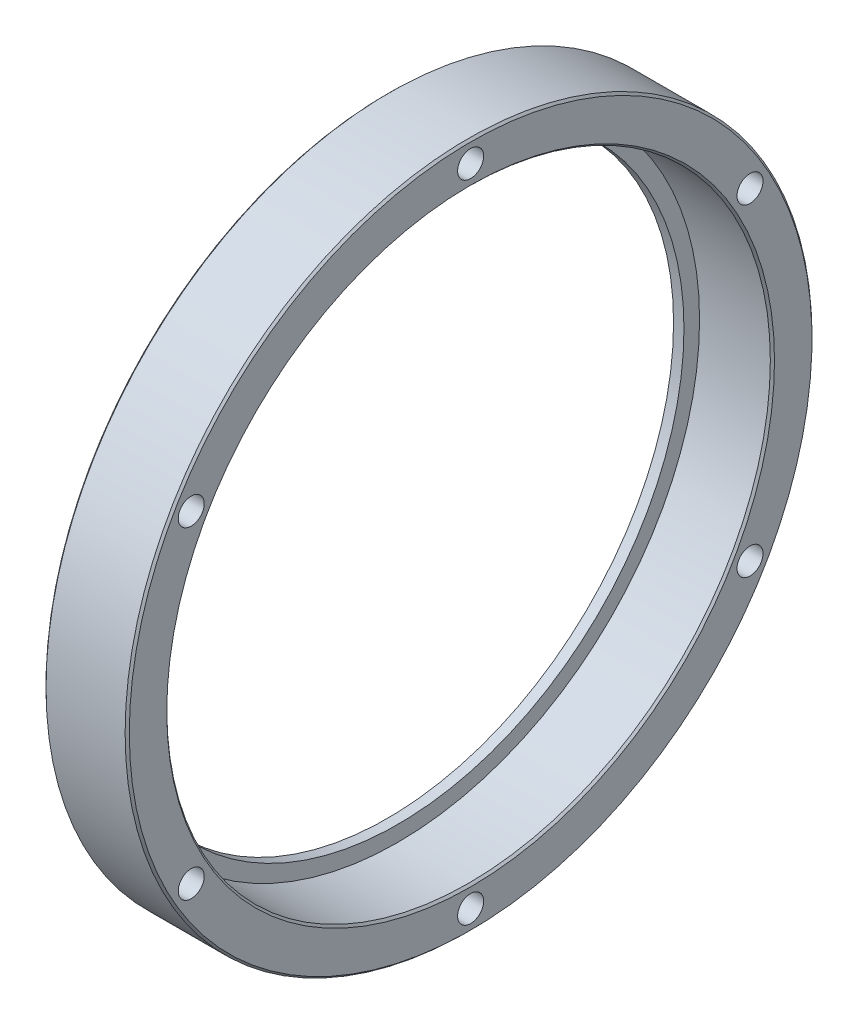
SolidWorks part; units mm, degrees
material "6061 合金"
ref_plane "前视基准面" through (0, 0, 0) normal (0, 0, 1) x (1, 0, 0)
ref_plane "上视基准面" through (0, 0, 0) normal (0, 1, 0) x (1, 0, 0)
ref_plane "右视基准面" through (0, 0, 0) normal (1, 0, 0) x (0, 0, -1)
sketch "草图1" plane through (0, 0, 0) normal (0, 0, 1) x (1, 0, 0)
  line L0 (0, 27.5) -> (0, 33)
  line L1 (0, 33) -> (8, 33)
  line L2 (8, 33) -> (8, 29)
  line L3 (8, 29) -> (1, 29)
  line L4 (1, 29) -> (1, 27.5)
  line L5 (1, 27.5) -> (0, 27.5)
  line L6 (0, 0) -> (56.1332, 0) construction
  dimension "D1" = 66
  dimension "D2" = 58
  dimension "D3" = 8
  dimension "D4" = 55
  dimension "D5" = 1
revolve "旋转1" add sketch "草图1" angle 360 about L6
sketch "草图2" plane through (8, 0, 0) normal (1, 0, 0) x (0, 0, -1)
  circle A0 centre (0, 0) radius 31 construction
  dimension "D1" = 62
hole_wizard "M3 螺纹孔1" positions "草图3" profile "草图4" tap size "M3" standard "GB" end condition through all
sketch "草图3" plane through (8, 0, 0) normal (1, 0, 0) x (0, 0, -1)
  line L0 (0, 31) -> (0, 0) construction
  circle A0 centre (0, 0) radius 31 construction
  point P0 (0, 31)
sketch "草图4" plane through (8, 31, 0) normal (0, 1, 0) x (0, 0, -1)
  line L0 (0, 0) -> (0, 8)
  line L1 (0, 8) -> (1.25, 8)
  line L2 (1.25, 8) -> (1.25, 0)
  line L5 (1.25, 0) -> (0, 0)
  line L11 (0, -6.35) -> (0, 107.95) construction
  dimension "通孔螺纹孔钻头直径" = 2.5
  dimension "通孔螺纹孔钻头深度" = 8
cosmetic thread "孔螺蚊线1" parameters "D2"=3
pattern_circular "阵列(圆周)1" count 6 over 360 about axis through (0, 0, 0) along (1, 0, 0) of "M3 螺纹孔1"
cosmetic thread "孔螺蚊线2" parameters "D2"=3
cosmetic thread "孔螺蚊线3" parameters "D2"=3
cosmetic thread "孔螺蚊线4" parameters "D2"=3
cosmetic thread "孔螺蚊线5" parameters "D2"=3
cosmetic thread "孔螺蚊线6" parameters "D2"=3
chamfer "倒角1" distance 0.2 angle 45 3 edges at (0, 0, 33) (8, 0, 33) (8, 0, 29)
